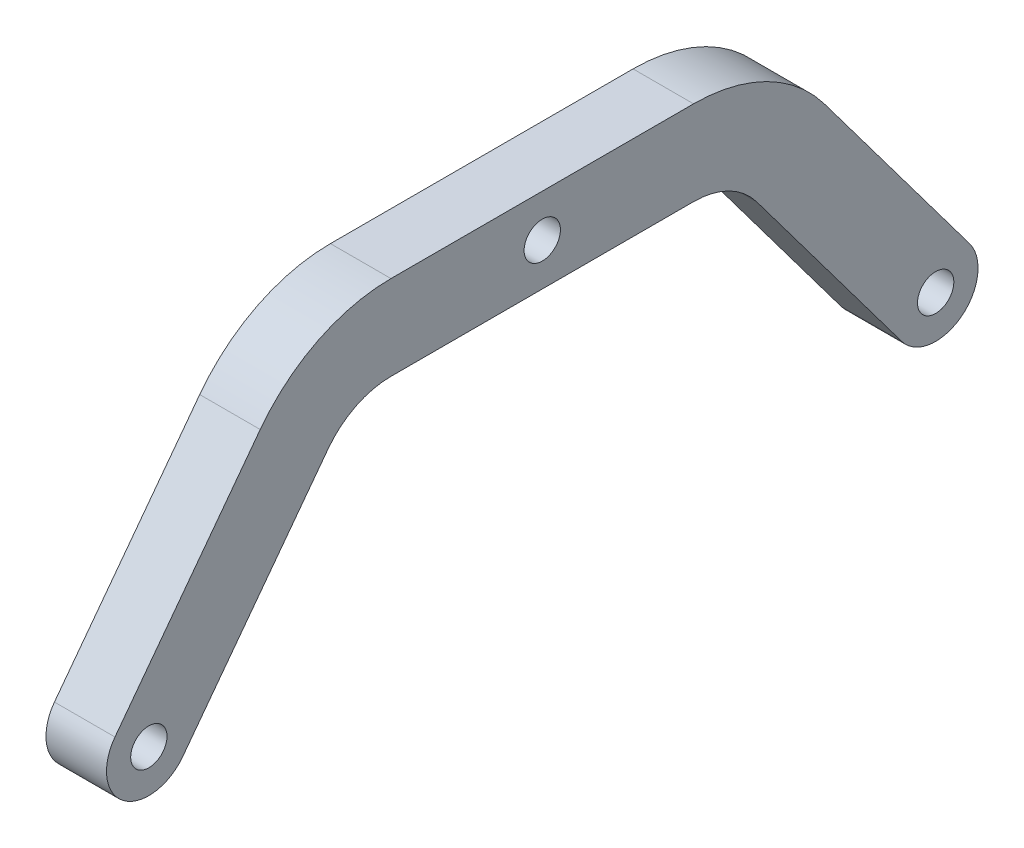
SolidWorks part; units mm, degrees
ref_plane "Front Plane" through (0, 0, 0) normal (0, 0, 1) x (1, 0, 0)
ref_plane "Top Plane" through (0, 0, 0) normal (0, 1, 0) x (1, 0, 0)
ref_plane "Right Plane" through (0, 0, 0) normal (1, 0, 0) x (0, 0, -1)
sketch "Sketch1" plane through (0, 0, 0) normal (1, 0, 0) x (0, 0, -1)
  line L0 (-12.5, 20) -> (12.5, 20) construction
  line L1 (-20.5, 16) -> (-32.5, 0) construction
  line L2 (0, 55) -> (0, -55) construction
  line L3 (20.5, 16) -> (32.5, 0) construction
  line L4 (23.3, 18.1) -> (35.3, 2.1)
  line L5 (-12.5, 23.5) -> (12.5, 23.5)
  line L6 (-23.3, 18.1) -> (-35.3, 2.1)
  line L7 (17.7, 13.9) -> (29.7, -2.1)
  line L8 (-12.5, 16.5) -> (12.5, 16.5)
  line L9 (-17.7, 13.9) -> (-29.7, -2.1)
  arc A0 (12.5, 20) -> (20.5, 16) centre (12.5, 10) cw construction
  arc A1 (-12.5, 20) -> (-20.5, 16) centre (-12.5, 10) ccw construction
  arc A2 (12.5, 23.5) -> (23.3, 18.1) centre (12.5, 10) cw
  arc A3 (-12.5, 23.5) -> (-23.3, 18.1) centre (-12.5, 10) ccw
  arc A4 (12.5, 16.5) -> (17.7, 13.9) centre (12.5, 10) cw
  arc A5 (-12.5, 16.5) -> (-17.7, 13.9) centre (-12.5, 10) ccw
  arc A6 (35.3, 2.1) -> (29.7, -2.1) centre (32.5, 0) cw
  arc A7 (-35.3, 2.1) -> (-29.7, -2.1) centre (-32.5, 0) ccw
  circle A8 centre (-32.5, 0) radius 1.5
  circle A9 centre (32.5, 0) radius 1.5
  circle A10 centre (0, 20) radius 1.5
  point P2 (0, 20)
  point P11 (17.5, 20)
  point P14 (-17.5, 20)
  dimension "D4" = 10
  dimension "D7" = 3
  dimension "D8" = 3
  dimension "D1" = 65
  dimension "D2" = 35
  dimension "D3" = 20
  dimension "D5" = 3.5
  dimension "D6" = 3.5
extrude "Boss-Extrude1" add sketch "Sketch1" along normal mid plane 5
